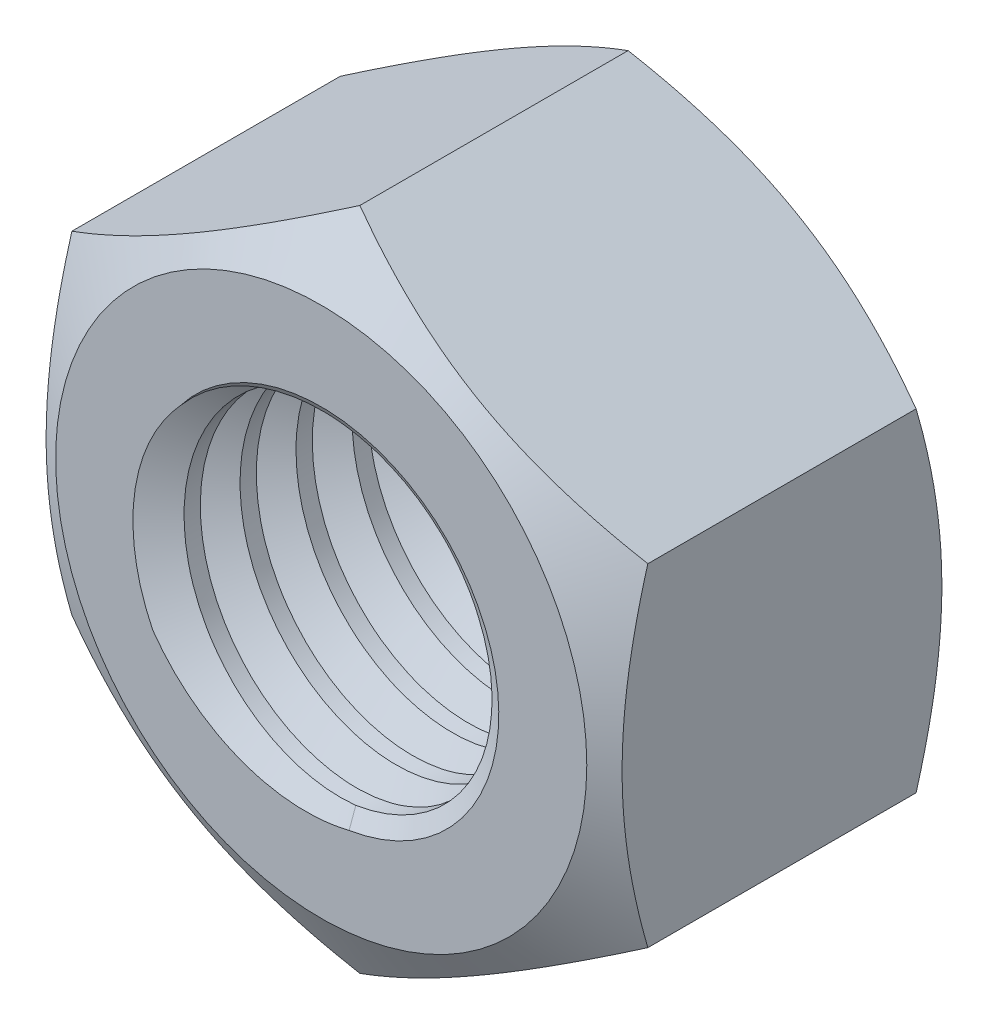
SolidWorks part; units mm, degrees
ref_plane "Płaszczyzna przednia" through (0, 0, 0) normal (0, 0, 1) x (1, 0, 0)
ref_plane "Płaszczyzna górna" through (0, 0, 0) normal (0, 1, 0) x (1, 0, 0)
ref_plane "Płaszczyzna prawa" through (0, 0, 0) normal (1, 0, 0) x (0, 0, -1)
sketch "Szkic1" plane through (0, 0, 0) normal (0, 0, 1) x (1, 0, 0)
  line L1 (0, 10.3923) -> (-9, 5.1962)
  line L2 (-9, 5.1962) -> (-9, -5.1962)
  line L3 (-9, -5.1962) -> (0, -10.3923)
  line L4 (0, -10.3923) -> (9, -5.1962)
  line L5 (9, -5.1962) -> (9, 5.1962)
  line L6 (9, 5.1962) -> (0, 10.3923)
  circle A0 centre (0, 0) radius 9 construction
  circle A1 centre (0, 0) radius 5.05
  dimension "D1" = 10.1
  dimension "D2" = 18
extrude "Dodanie-wyciągnięcie1" add sketch "Szkic1" along normal blind 10.8
sketch "Szkic2" plane through (0, 0, 10.8) normal (0, 0, 1) x (1, 0, 0)
  circle A0 centre (0, 0) radius 8.3
extrude "Wytnij-wyciągnięcie1" cut sketch "Szkic2" against normal through all draft 60 flip side to cut
sketch "Szkic3" plane through (0, 0, 0) normal (0, 0, -1) x (-1, 0, 0)
  circle A0 centre (0, 0) radius 8.3
extrude "Wytnij-wyciągnięcie3" cut sketch "Szkic3" against normal through all draft 60 flip side to cut contours A0
chamfer "Sfazowanie2" distance 0.5 angle 30 2 edges at (5.05, 0, 10.8) (5.05, 0, 0)
sketch "Szkic5" plane through (0, 0, 0) normal (0, 0, -1) x (-1, 0, 0)
  circle A0 centre (0, 0) radius 5.05
curve "Helisa/Spirala1" pitch 1.75 height 13 turns 7.4286
sketch "Szkic9" plane through (0, 0, 0) normal (0, 1, 0) x (1, 0, 0)
  line L1 (-6.125, 1.6) -> (-4.5125, 0.669)
  line L2 (-4.5125, 0.669) -> (-4.5125, 2.531)
  line L3 (-4.5125, 2.531) -> (-6.125, 1.6)
  line L4 (0, -9.592) -> (0, -1.208) construction
  circle A0 centre (-5.05, 1.6) radius 1.075 construction
  point P8 (0, -5.4)
  dimension "D1" = 2.15
  dimension "D2" = 1.6
  dimension "D3" = 5.05
sweep "Wycięcie-wyciągnięcie po ścieżce4" cut profiles "Szkic9" path "Helisa/Spirala1"
